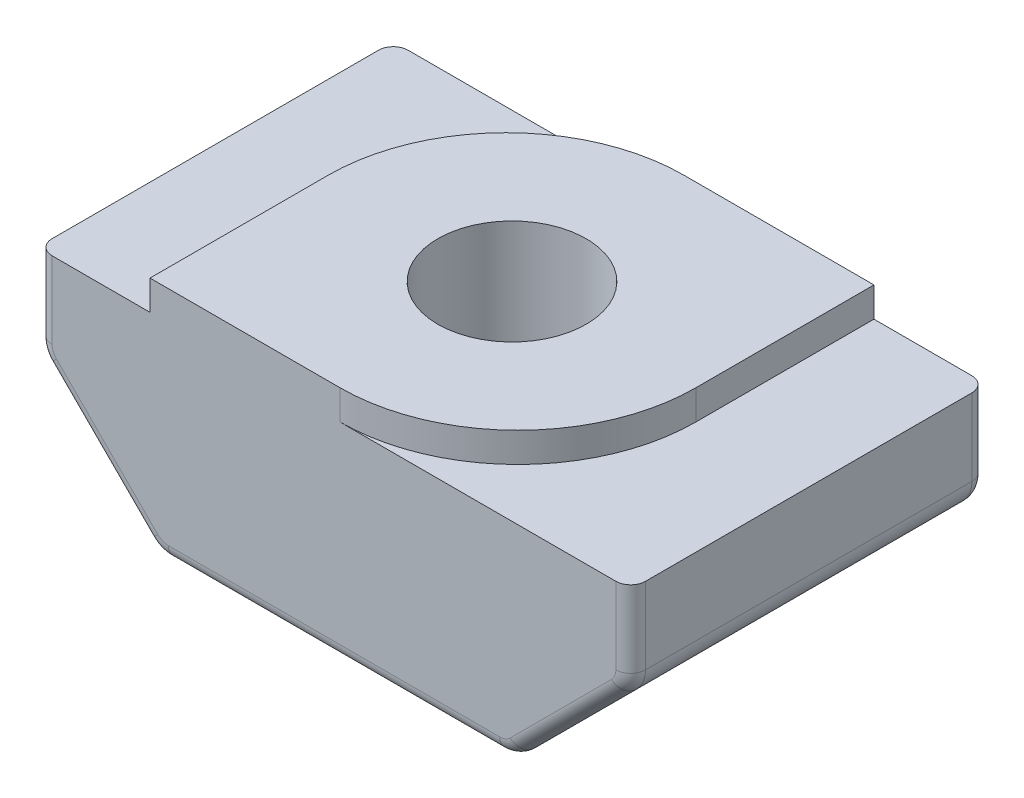
SolidWorks part; units mm, degrees
material "1023 Carbon Steel Sheet (SS)"
ref_plane "Front" through (0, 0, 0) normal (0, 0, 1) x (1, 0, 0)
ref_plane "Top" through (0, 0, 0) normal (0, 1, 0) x (1, 0, 0)
ref_plane "Right" through (0, 0, 0) normal (1, 0, 0) x (0, 0, -1)
sketch "Sketch1" plane through (0, 0, 0) normal (0, 0, 1) x (1, 0, 0)
  line L0 (3.1, 0) -> (-3.1, 0)
  line L1 (-3.1, 0) -> (-3.1, -0.5)
  line L2 (-3.1, -0.5) -> (-5, -0.5)
  line L3 (-5, -0.5) -> (-5, -2)
  line L4 (-5, -2) -> (-3, -4)
  line L5 (-3, -4) -> (3, -4)
  line L6 (0, -4) -> (0, 0) construction
  line L7 (-21.4155, -64.3546) -> (311.9179, -64.3546) construction
  line L8 (5, -2) -> (3, -4)
  line L9 (5, -0.5) -> (5, -2)
  line L10 (3.1, -0.5) -> (5, -0.5)
  line L11 (3.1, 0) -> (3.1, -0.5)
  point P4 (0, 0)
  dimension "D1" = 10
  dimension "D2" = 6.2
  dimension "D3" = 3.5
  dimension "D4" = 0.5
  dimension "D5" = 135
  dimension "D6" = 1.5
extrude "Boss-Extrude1" add sketch "Sketch1" along normal blind 6
sketch "Sketch2" plane through (0, 0, 0) normal (0, 1, 0) x (1, 0, 0)
  line L0 (-3.1, 0) -> (3.1, -6) construction
  circle A0 centre (0, -3) radius 1.5
  dimension "D1" = 3
hole_wizard "M3 Tapped Hole1" positions "Sketch4" profile "Sketch3" tap size "M3" standard "ISO" end condition through all
sketch "Sketch4" plane through (0, 0, 0) normal (0, 1, 0) x (-1, 0, 0)
  point P0 (0, 3)
sketch "Sketch3" plane through (0, 0, 3) normal (1, 0, 0) x (0, 0, 1)
  line L0 (0, 0) -> (0, 4)
  line L1 (0, 4) -> (1.25, 4)
  line L2 (1.25, 4) -> (1.25, 0)
  line L5 (1.25, 0) -> (0, 0)
  line L11 (0, -6.35) -> (0, 107.95) construction
  dimension "Thru Tap Drill Dia." = 2.5
  dimension "Thru Tap Drill Depth" = 4
cosmetic thread "Hole Thread1" parameters "D2"=3
fillet "Fillet1" radius 3 2 edges at (-3.1, -0.25, 0) (3.1, -0.25, 6)
fillet "Fillet2" radius 0.5 4 edges at (5, -2, 3) (3, -4, 3) (-5, -2, 3) (-3, -4, 3)
fillet "Fillet3" radius 0.25 18 edges at (-5, -1.1464, 0) (-4.9619, -1.9842, 0) (-4, -3, 0) (-2.9842, -3.9619, 0) (5, -1.1464, 0) (4.9619, -1.9842, 0) (4, -3, 0) (2.9842, -3.9619, 0) (-5, -1.1464, 6) (-4.9619, -1.9842, 6) (-4, -3, 6) (-2.9842, -3.9619, 6) (5, -1.1464, 6) (4.9619, -1.9842, 6) (4, -3, 6) (2.9842, -3.9619, 6) (0, -4, 0) (0, -4, 6)
